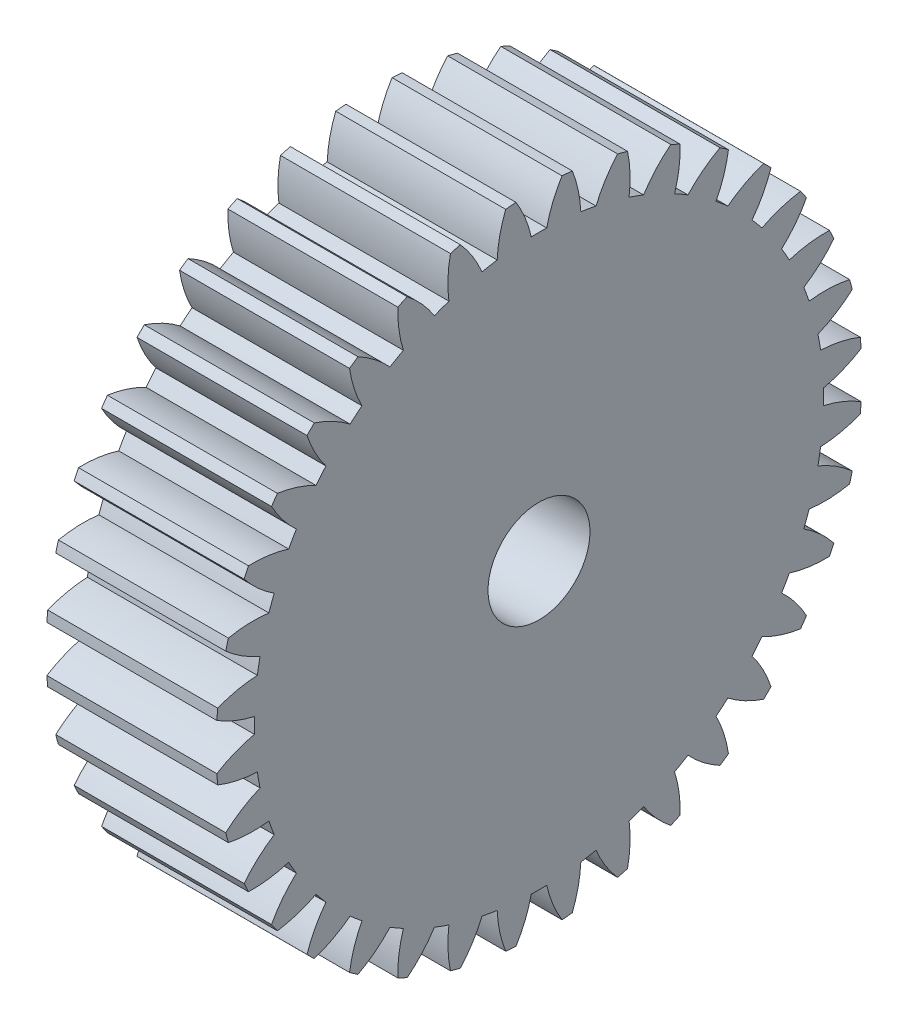
SolidWorks part; units mm, degrees
ref_plane "Plane1" through (0, 0, 0) normal (0, 0, 1) x (1, 0, 0)
ref_plane "Plane2" through (0, 0, 0) normal (0, 1, 0) x (1, 0, 0)
ref_plane "Plane3" through (0, 0, 0) normal (1, 0, 0) x (0, 0, -1)
other "Configuration Table"
sketch "HoldingSke" plane through (0, 0, 0) normal (0, 1, 0) x (1, 0, 0)
  line L0 (0, 0) -> (0.809, -0.5878)
  line L1 (-15, 0) -> (100, 0) construction
  line L2 (0, 0) -> (-2.1039, 2.3779)
  line L3 (0, 0) -> (-11.863, 4.5341)
  line L4 (0, 0) -> (6.9867, 5.0761)
  line L5 (0, 0) -> (-46.8476, -17.4728)
  line L6 (0, 0) -> (-8.2896, -5.593)
  line L7 (-2.1039, 2.3779) -> (8.6586, 51.2059)
  line L8 (-76.2, 54.61) -> (-75.2, 54.61)
  line L9 (-71.009, 38.7566) -> (-53.1078, 45.2721)
  line L10 (-76.2, 71.12) -> (104.1128, 71.12)
  line L11 (0, 0) -> (-10, 0)
  line L12 (-76.2, 101.6) -> (-76.162, 101.6)
  line L13 (24.9733, 27.94) -> (52.9518, 28.4284)
  line L14 (24.9733, 27.94) -> (24.9743, 27.94)
  line L15 (24.9733, 27.94) -> (100.4006, 29.5858)
  line L16 (-63.627, -1) -> (-12.827, -1)
  circle A0 centre (0, 0) radius 3
  circle A1 centre (0, 0) radius 16.749
  circle A2 centre (0, 0) radius 37.5
  circle A3 centre (0, 0) radius 3
  dimension "MHD" = 33.498
  dimension "Hub_dia" = 75
  dimension "Bore" = 6
  dimension "MBD" = 6
  dimension "Num_teeth" = 36
  dimension "Pitch" = 1
  dimension "Overall_len" = 50
  dimension "Show_teeth" = 36
  dimension "Thickness" = 10
  dimension "OAL" = 50.0001
  dimension "T_dim" = 1
  dimension "Ap" = 20
  dimension "H" = 19.05
  dimension "Pitch_radius" = 180.3128
  dimension "Width" = 10
  dimension "Backlash" = 0.038
  dimension "Addendum_fac" = 1
  dimension "Dedendum_fac" = 1.25
  dimension "Clearance_fac" = 0.25
  dimension "Dedendum_add" = 0.001
  dimension "Module" = 1
sketch "BasProSke" plane through (0, 0, 0) normal (0, 1, 0) x (1, 0, 0)
  line L0 (-10, 0) -> (60, 0) construction
  line L1 (0, 0) -> (0, 19)
  line L2 (0, 0) -> (10, 0)
  line L3 (10, 0) -> (10, 19)
  line L4 (10, 19) -> (0, 19)
  dimension "Thickness" = 10
  dimension "Diameter" = 38
revolve "Base-Revolve" add sketch "BasProSke" angle 360 about L0
sketch "TooCutSke" plane through (0, 0, 0) normal (1, 0, 0) x (0, 0, -1)
  line L1 (0, 0) -> (0, 107) construction
  line L2 (0, 0) -> (-0.8516, 17.9798) construction
  line L3 (0, 0) -> (-3.1351, 35.8344) construction
  line L4 (-0.8516, 17.9798) -> (-1.5676, 17.9172) construction
  arc A0 (0.4547, 16.7428) -> (-0.4547, 16.7428) centre (0, 0) ccw
  arc A1 (1.3689, 18.9761) -> (-1.3689, 18.9761) centre (0, 0) ccw
  circle A2 centre (0, 0) radius 18 construction
  circle A3 centre (0, 0) radius 16.9145 construction
  arc A4 (-0.4547, 16.7428) -> (-1.3689, 18.9761) centre (-7.4808, 15.1702) ccw
  arc A5 (1.3689, 18.9761) -> (0.4547, 16.7428) centre (7.4808, 15.1702) ccw
  dimension "Root_dia" = 33.498
  dimension "Overcut_dia" = 38.0508
  dimension "Pitch_dia" = 36
  dimension "Base_dia" = 33.8289
  dimension "Flank_rad" = 7.2
  dimension "Half_ang" = 5
  dimension "Half_CT" = 0.7186
extrude "ToothCut" cut sketch "TooCutSke" along normal through all
fillet "Breaks" [suppressed] radius 0.02
fillet "RootFillets" [suppressed] radius 0.251
pattern_circular "TeethCuts" count 36 every 10 about axis through (-10, 0, 0) along (1, 0, 0) of "ToothCut", "RootFillets", "Breaks"
sketch "HubNeaOneSke" plane through (0, 0, 0) normal (-1, 0, 0) x (0, 0, 1)
  circle A0 centre (0, 0) radius 16.749
  dimension "Diameter" = 33.498
extrude "HubNearOne" [suppressed] add sketch "HubNeaOneSke" along normal blind 40.0001
sketch "HubNeaBotSke" plane through (0, 0, 0) normal (-1, 0, 0) x (0, 0, 1)
  circle A0 centre (0, 0) radius 16.749
  dimension "Diameter" = 33.498
extrude "HubNearBoth" [suppressed] add sketch "HubNeaBotSke" along normal blind 20
ref_plane "FarPln" through (10, 0, 0) normal (1, 0, 0) x (0, 0, -1)
sketch "HubFarSke" plane through (10, 0, 0) normal (1, 0, 0) x (0, 0, -1)
  circle A0 centre (0, 0) radius 16.749
  dimension "Diameter" = 33.498
extrude "HubFar" [suppressed] add sketch "HubFarSke" along normal blind 20
sketch "BorSke" plane through (0, 0, 0) normal (1, 0, 0) x (0, 0, -1)
  circle A0 centre (0, 0) radius 3
  dimension "Diameter" = 6
extrude "Bore" cut sketch "BorSke" along normal mid plane 100.0001
sketch "KeySke" plane through (0, 0, 0) normal (1, 0, 0) x (0, 0, -1)
  line L0 (-1, 0) -> (-1, 4)
  line L1 (-1, 4) -> (1, 4)
  line L2 (1, 4) -> (1, 0)
  line L3 (0, 0) -> (0, 34) construction
  line L4 (-1, 0) -> (1, 0)
  dimension "Offset" = 4
  dimension "Width" = 2
extrude "Keyway" [suppressed] cut sketch "KeySke" along normal mid plane 100.0001
pattern_circular "Keyway2" [suppressed] count 2 every 90 about axis through (-10, 0, 0) along (1, 0, 0)
equation "' \"Module@HoldingSke\" = 6.35"
equation "' \"Num_teeth@HoldingSke\" = 12"
equation "' \"Ap@HoldingSke\" =  20"
equation "' \"Ap@HoldingSke\" = 20"
equation "' \"Width@HoldingSke\" = 0.5 * 25.4"
equation "' \"Hub_dia@HoldingSke\"= 1 * 25.4"
equation "' \"Hub_dia@HoldingSke\" = 1 * 25.4"
equation "' \"Overall_len@HoldingSke\" = 1.0 * 25.4"
equation "' \"Bore@HoldingSke\" = 0.75 * 25.4"
equation "' \"T_dim@HoldingSke\" = 0.1 * 25.4"
equation "' \"Width@KeySke\" = 0.25 * 25.4"
equation "' \"Show_teeth@HoldingSke\" = 13"
equation "' \"Backlash@HoldingSke\" = 0.009 * 25.4"
equation "' \"Addendum_fac@HoldingSke\" = 1.0"
equation "' \"Dedendum_fac@HoldingSke\" = 1.25"
equation "' \"Dedendum_add@HoldingSke\" = 0.00005 * 25.4"
equation "' \"Clearance_fac@HoldingSke\" = 0.25"
equation "\"Pitch@HoldingSke\" = 1 / \"Module@HoldingSke\""
equation "\"Overcut_dia@TooCutSke\" = (\"Num_teeth@HoldingSke\" + 2 * \"Addendum_fac@HoldingSke\") / \"Pitch@HoldingSke\" + 0.002 * 25.4"
equation "\"Pitch_dia@TooCutSke\" = \"Num_teeth@HoldingSke\" / \"Pitch@HoldingSke\""
equation "\"Base_dia@TooCutSke\" = \"Num_teeth@HoldingSke\" / \"Pitch@HoldingSke\" * cos((\"Ap@HoldingSke\"  * 3.14159265 / 180))"
equation "\"Root_dia@TooCutSke\" = (\"Num_teeth@HoldingSke\" + 2) / \"Pitch@HoldingSke\" - 2 * (\"Addendum_fac@HoldingSke\" + \"Dedendum_fac@HoldingSke\") / \"Pitch@HoldingSke\" - \"Dedendum_add@HoldingSke\" * 2"
equation "\"Half_ang@TooCutSke\" = 180 / \"Num_teeth@HoldingSke\""
equation "\"Half_CT@TooCutSke\" = \"Num_teeth@HoldingSke\" / \"Pitch@HoldingSke\" * sin((3.14159265 / 2 / \"Num_teeth@HoldingSke\")) / 2 - 7 * \"Backlash@HoldingSke\" / 4"
equation "\"Flank_rad@TooCutSke\" = \"Num_teeth@HoldingSke\" / \"Pitch@HoldingSke\" / 5"
equation "\"Radius@RootFillets\" = \"Clearance_fac@HoldingSke\" / \"Pitch@HoldingSke\" + \"Dedendum_add@HoldingSke\""
equation "\"Break_rad@Breaks\" = 0.02 / \"Pitch@HoldingSke\""
equation "\"Thickness@HoldingSke\" = \"Width@HoldingSke\""
equation "\"OAL@HoldingSke\" = \"Thickness@HoldingSke\""
equation "\"MHD@HoldingSke\" = (\"Num_teeth@HoldingSke\" + 2) / \"Pitch@HoldingSke\" - 2 * (\"Addendum_fac@HoldingSke\" + \"Dedendum_fac@HoldingSke\")  / \"Pitch@HoldingSke\" - \"Dedendum_add@HoldingSke\" * 2"
equation "\"MBD@HoldingSke\" = (\"Num_teeth@HoldingSke\" + 2) / \"Pitch@HoldingSke\" - 2 * (\"Addendum_fac@HoldingSke\" + \"Dedendum_fac@HoldingSke\")  / \"Pitch@HoldingSke\" - \"Dedendum_add@HoldingSke\" * 2 - 0.002 * 25.4"
equation "\"MHD@HoldingSke\" = ((sgn( \"MHD@HoldingSke\" - \"Hub_dia@HoldingSke\" )-1)*( \"MHD@HoldingSke\" - \"Hub_dia@HoldingSke\" ))/-2+ \"Hub_dia@HoldingSke\""
equation "\"MBD@HoldingSke\" = ((sgn( \"MBD@HoldingSke\" - \"Bore@HoldingSke\" )-1)*( \"MBD@HoldingSke\" - \"Bore@HoldingSke\" ))/-2+ \"Bore@HoldingSke\""
equation "\"OAL@HoldingSke\" = ((sgn( \"OAL@HoldingSke\" - \"Overall_len@HoldingSke\" )+1)*( \"OAL@HoldingSke\" - \"Overall_len@HoldingSke\" ))/2 + \"Overall_len@HoldingSke\" + 0.000002 * 25.4"
equation "\"Num_teeth@TeethCuts\" = int( \"Show_teeth@HoldingSke\" ) + 1"
equation "\"Num_teeth@TeethCuts\" = ((sgn( \"Num_teeth@TeethCuts\" - \"Num_teeth@HoldingSke\" )-1)*( \"Num_teeth@TeethCuts\" - \"Num_teeth@HoldingSke\" ))/-2+ \"Num_teeth@HoldingSke\""
equation "\"Num_teeth@TeethCuts\" = ((sgn( \"Num_teeth@TeethCuts\" - 2.0)+1)*( \"Num_teeth@TeethCuts\" - 2.0))/2 +2.0"
equation "\"Angle@TeethCuts\" = 360.0 / \"Num_teeth@HoldingSke\""
equation "\"Diameter@BasProSke\" = (\"Num_teeth@HoldingSke\" + 2 * \"Addendum_fac@HoldingSke\") / \"Pitch@HoldingSke\""
equation "\"Thickness@BasProSke\"  = \"Thickness@HoldingSke\""
equation "' \"Fillet_rad@BasProSke\" =  \"Thickness@HoldingSke\" * 0.05"
equation "' \"Fillet_rad@BasProSke\" = \"Thickness@HoldingSke\" * 0.05"
equation "\"MHD@HoldingSke\" = ((sgn( \"MHD@HoldingSke\" - \"Root_dia@TooCutSke\" )-1)*( \"MHD@HoldingSke\" - \"Root_dia@TooCutSke\" ))/-2+ \"Root_dia@TooCutSke\""
equation "\"Diameter@HubNeaOneSke\" = \"MHD@HoldingSke\""
equation "\"Length@HubNearOne\" = \"OAL@HoldingSke\" - \"Thickness@BasProSke\""
equation "\"Diameter@HubNeaBotSke\" = \"MHD@HoldingSke\""
equation "\"Length@HubNearBoth\" = ( \"OAL@HoldingSke\" - \"Thickness@BasProSke\" ) / 2.0"
equation "\"Thickness@FarPln\" = \"Thickness@BasProSke\""
equation "\"Diameter@HubFarSke\" = \"MHD@HoldingSke\""
equation "\"Length@HubFar\" = ( \"OAL@HoldingSke\" - \"Thickness@BasProSke\" ) / 2.0"
equation "\"Diameter@BorSke\" = \"MBD@HoldingSke\""
equation "\"D1@Bore\" = \"OAL@HoldingSke\" * 2.0"
equation "\"D1@Keyway\" = \"OAL@HoldingSke\" * 2.0"
equation "\"Offset@KeySke\" = \"T_dim@HoldingSke\" + \"MBD@HoldingSke\" / 2.0"
